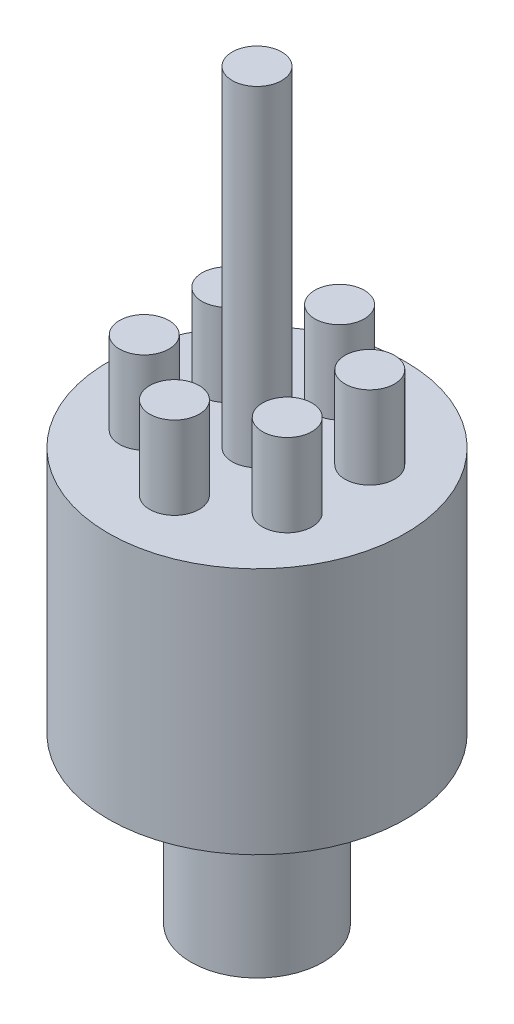
SolidWorks part; units mm, degrees
ref_plane "Front" through (0, 0, 0) normal (0, 0, 1) x (1, 0, 0)
ref_plane "Top" through (0, 0, 0) normal (0, 1, 0) x (1, 0, 0)
ref_plane "Right" through (0, 0, 0) normal (1, 0, 0) x (0, 0, -1)
sketch "Sketch1" plane through (0, 0, 0) normal (1, 0, 0) x (0, 0, -1)
  line L0 (0, 0) -> (-8, 0)
  line L1 (-8, 0) -> (-8, 20)
  line L2 (-8, 20) -> (-18, 20)
  line L3 (-18, 20) -> (-18, 50)
  line L4 (-18, 50) -> (-3, 50)
  line L5 (-3, 50) -> (-3, 90)
  line L6 (-3, 90) -> (0, 90)
  line L7 (0, 90) -> (0, 0)
  dimension "D1" = 90
  dimension "D2" = 40
  dimension "D3" = 30
  dimension "D4" = 8
  dimension "D5" = 18
  dimension "D6" = 3
revolve "Revolve1" add sketch "Sketch1" angle 360 about L7
sketch "Sketch2" plane through (0, 50, 0) normal (0, 1, 0) x (1, 0, 0)
  line L0 (0, 10) -> (0, 0) construction
  circle A0 centre (0, 10) radius 3
  dimension "D1" = 6
  dimension "D2" = 10
extrude "Boss-Extrude1" add sketch "Sketch2" along normal blind 10
pattern_circular "CirPattern1" count 6 over 360 about axis through (0, 0, 0) along (0, 1, 0) of "Boss-Extrude1"
